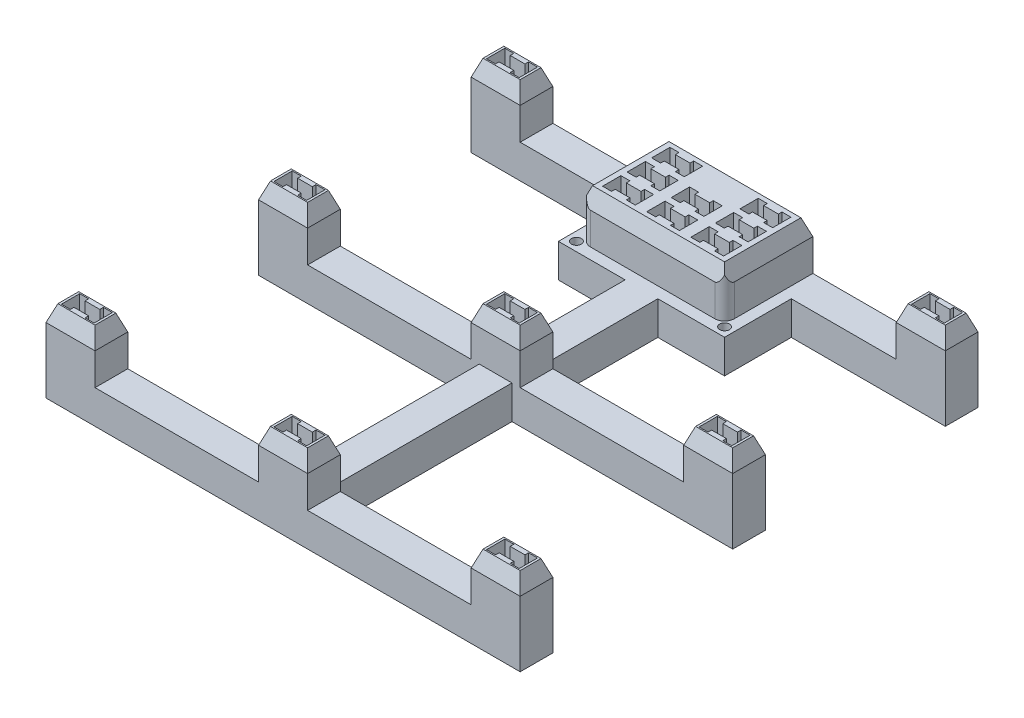
SolidWorks part; units mm, degrees
ref_plane "Front Plane" through (0, 0, 0) normal (0, 0, 1) x (1, 0, 0)
ref_plane "Top Plane" through (0, 0, 0) normal (0, 1, 0) x (1, 0, 0)
ref_plane "Right Plane" through (0, 0, 0) normal (1, 0, 0) x (0, 0, -1)
sketch "Sketch1" plane through (0, 0, 0) normal (0, 1, 0) x (1, 0, 0)
  line L0 (50.5, 130) -> (0, 130)
  line L1 (0, 140) -> (0, 130)
  line L2 (0, 140) -> (145, 140)
  line L4 (145, 130) -> (145, 140)
  line L5 (94.5, 130) -> (145, 130)
  line L6 (50.5, 130) -> (50.5, 113)
  line L7 (50.5, 113) -> (67.5, 113)
  line L8 (94.5, 113) -> (94.5, 130)
  line L9 (77.5, 113) -> (94.5, 113)
  line L10 (67.5, 113) -> (67.5, 75)
  line L11 (77.5, 75) -> (77.5, 113)
  line L12 (67.5, 75) -> (0, 75)
  line L13 (0, 65) -> (0, 75)
  line L14 (0, 65) -> (67.5, 65)
  line L15 (145, 75) -> (77.5, 75)
  line L16 (145, 65) -> (145, 75)
  line L17 (77.5, 65) -> (145, 65)
  line L18 (67.5, 65) -> (67.5, 10)
  line L19 (77.5, 10) -> (77.5, 65)
  line L20 (67.5, 10) -> (0, 10)
  line L21 (0, 10) -> (0, 0)
  line L22 (0, 0) -> (145, 0)
  line L24 (77.5, 10) -> (145, 10)
  line L25 (145, 10) -> (145, 0)
  dimension "D1" = 10
  dimension "D2" = 145
  dimension "D3" = 50.5
  dimension "D4" = 17
  dimension "D5" = 17
  dimension "D6" = 55
  dimension "D7" = 55
extrude "Boss-Extrude1" add sketch "Sketch1" along normal blind 10
sketch "Sketch2" plane through (0, 10, 0) normal (0, 1, 0) x (1, 0, 0)
  line L0 (145, 10) -> (77.5, 10) construction
  line L1 (145, 0) -> (130, 0)
  line L2 (145, 0) -> (145, 10)
  line L3 (145, 10) -> (130, 10)
  line L4 (130, 0) -> (130, 10)
  line L6 (80, 0) -> (65, 0)
  line L7 (80, 0) -> (80, 10)
  line L8 (80, 10) -> (65, 10)
  line L9 (65, 0) -> (65, 10)
  line L10 (67.5, 10) -> (0, 10) construction
  line L11 (0, 0) -> (15, 0)
  line L12 (0, 0) -> (0, 10)
  line L13 (0, 10) -> (15, 10)
  line L14 (15, 0) -> (15, 10)
  line L15 (67.5, 75) -> (0, 75) construction
  line L16 (0, 65) -> (15, 65)
  line L17 (0, 65) -> (0, 75)
  line L18 (0, 75) -> (15, 75)
  line L19 (15, 65) -> (15, 75)
  line L20 (145, 75) -> (77.5, 75) construction
  line L21 (145, 65) -> (130, 65)
  line L22 (145, 65) -> (145, 75)
  line L23 (145, 75) -> (130, 75)
  line L24 (130, 65) -> (130, 75)
  line L25 (77.5, 65) -> (145, 65) construction
  line L26 (80, 65) -> (65, 65)
  line L27 (80, 65) -> (80, 75)
  line L28 (80, 75) -> (65, 75)
  line L29 (65, 65) -> (65, 75)
  line L30 (145, 140) -> (0, 140) construction
  line L31 (145, 130) -> (130, 130)
  line L32 (145, 130) -> (145, 140)
  line L33 (145, 140) -> (130, 140)
  line L34 (130, 130) -> (130, 140)
  line L35 (0, 0) -> (145, 0) construction
  line L36 (0, 130) -> (15, 130)
  line L37 (0, 130) -> (0, 140)
  line L38 (0, 140) -> (15, 140)
  line L39 (15, 130) -> (15, 140)
  line L40 (50.5, 140) -> (94.5, 140)
  line L41 (50.5, 113) -> (94.5, 113)
  line L42 (50.5, 113) -> (50.5, 140)
  line L44 (94.5, 113) -> (94.5, 140)
  point P62 (72.5, 0)
  dimension "D1" = 15
extrude "Boss-Extrude2" add sketch "Sketch2" along normal blind 10
sketch "Sketch3" plane through (0, 20, 0) normal (0, 1, 0) x (1, 0, 0)
  line L0 (0, 140) -> (0, 130) construction
  line L1 (0, 130) -> (15, 130) construction
  line L2 (15, 130) -> (15, 140) construction
  line L3 (15, 140) -> (0, 140) construction
  line L4 (145, 0) -> (145, 10)
  line L5 (145, 10) -> (130, 10)
  line L6 (130, 10) -> (130, 0)
  line L7 (130, 0) -> (145, 0)
  line L8 (145, 0) -> (145, 10)
  line L9 (145, 10) -> (130, 10)
  line L10 (130, 10) -> (130, 0)
  line L11 (130, 0) -> (145, 0)
  line L12 (145, 130) -> (145, 140) construction
  line L13 (145, 140) -> (130, 140) construction
  line L14 (130, 140) -> (130, 130) construction
  line L15 (130, 130) -> (145, 130) construction
  line L16 (145, 65) -> (145, 75) construction
  line L17 (145, 75) -> (130, 75) construction
  line L18 (130, 75) -> (130, 65) construction
  line L19 (130, 65) -> (145, 65) construction
  line L20 (80, 65) -> (80, 75) construction
  line L21 (80, 75) -> (65, 75) construction
  line L22 (65, 75) -> (65, 65) construction
  line L23 (65, 65) -> (80, 65) construction
  line L24 (0, 75) -> (0, 65) construction
  line L25 (0, 65) -> (15, 65) construction
  line L26 (15, 65) -> (15, 75) construction
  line L27 (15, 75) -> (0, 75) construction
  line L28 (0, 10) -> (0, 0) construction
  line L29 (0, 0) -> (15, 0) construction
  line L30 (15, 0) -> (15, 10) construction
  line L31 (15, 10) -> (0, 10) construction
  line L32 (80, 0) -> (80, 10) construction
  line L33 (80, 10) -> (65, 10) construction
  line L34 (65, 10) -> (65, 0) construction
  line L35 (65, 0) -> (80, 0) construction
  line L36 (0, 140) -> (0, 130)
  line L37 (0, 130) -> (15, 130)
  line L38 (15, 130) -> (15, 140)
  line L39 (15, 140) -> (0, 140)
  line L40 (145, 130) -> (145, 140)
  line L41 (145, 140) -> (130, 140)
  line L42 (130, 140) -> (130, 130)
  line L43 (130, 130) -> (145, 130)
  line L44 (145, 65) -> (145, 75)
  line L45 (145, 75) -> (130, 75)
  line L46 (130, 75) -> (130, 65)
  line L47 (130, 65) -> (145, 65)
  line L48 (80, 65) -> (80, 75)
  line L49 (80, 75) -> (65, 75)
  line L50 (65, 75) -> (65, 65)
  line L51 (65, 65) -> (80, 65)
  line L52 (0, 75) -> (0, 65)
  line L53 (0, 65) -> (15, 65)
  line L54 (15, 65) -> (15, 75)
  line L55 (15, 75) -> (0, 75)
  line L56 (0, 10) -> (0, 0)
  line L57 (0, 0) -> (15, 0)
  line L58 (15, 0) -> (15, 10)
  line L59 (15, 10) -> (0, 10)
  line L60 (80, 0) -> (80, 10)
  line L61 (80, 10) -> (65, 10)
  line L62 (65, 10) -> (65, 0)
  line L63 (65, 0) -> (80, 0)
  line L68 (50.5, 140) -> (50.5, 113)
  line L69 (50.5, 113) -> (94.5, 113)
  line L70 (94.5, 113) -> (94.5, 140)
  line L71 (94.5, 140) -> (50.5, 140)
  line L72 (50.5, 140) -> (50.5, 113)
  line L73 (50.5, 113) -> (94.5, 113)
  line L74 (94.5, 113) -> (94.5, 140)
  line L75 (94.5, 140) -> (50.5, 140)
  dimension "D1" = 0
  dimension "D2" = 0
extrude "Boss-Extrude3" add sketch "Sketch3" along normal blind 5 draft 20
sketch "Sketch4" plane through (0, 25, 0) normal (0, 1, 0) x (1, 0, 0)
  line L0 (94.5, 140) -> (50.5, 140) construction
  line L1 (89, 140) -> (56, 140)
  line L2 (89, 140) -> (89, 138.1801)
  line L3 (89, 138.1801) -> (56, 138.1801)
  line L4 (56, 140) -> (56, 138.1801)
  line L5 (92.6802, 138.1801) -> (52.3199, 138.1801) construction
  point P9 (72.5, 140)
  dimension "D1" = 33
extrude "Cut-Extrude1" cut sketch "Sketch4" against normal blind 15
sketch "Sketch5" plane through (0, 25, 0) normal (0, 1, 0) x (1, 0, 0)
  line L1 (142.5, 3.3) -> (132.5, 3.3)
  line L2 (142.5, 3.3) -> (142.5, 6.7)
  line L3 (142.5, 6.7) -> (132.5, 6.7)
  line L4 (132.5, 3.3) -> (132.5, 6.7)
  line L6 (132.5, 5) -> (131.8199, 5) construction
  line L7 (131.8199, 8.1802) -> (131.8199, 1.8199) construction
  line L8 (137.5, 6.7) -> (137.5, 8.1802) construction
  line L9 (143.1802, 8.1802) -> (131.8199, 8.1802) construction
  dimension "D1" = 3.4
  dimension "D2" = 10
extrude "Cut-Extrude2" cut sketch "Sketch5" against normal blind 7.75
sketch "Sketch7" plane through (0, 25, 0) normal (0, 1, 0) x (1, 0, 0)
  line L0 (142.5, 6.7) -> (132.5, 6.7) construction
  line L1 (132.5, 6.7) -> (135.25, 6.7)
  line L2 (132.5, 6.7) -> (132.5, 7.8)
  line L3 (132.5, 7.8) -> (135.25, 7.8)
  line L4 (135.25, 6.7) -> (135.25, 7.8)
  line L5 (132.5, 6.7) -> (132.5, 3.3) construction
  line L6 (132.5, 6.7) -> (132.5, 3.3) construction
  line L8 (132.5, 3.3) -> (135.25, 3.3)
  line L9 (132.5, 3.3) -> (132.5, 2.2)
  line L10 (132.5, 2.2) -> (135.25, 2.2)
  line L11 (135.25, 3.3) -> (135.25, 2.2)
  line L12 (142.5, 6.7) -> (139.75, 6.7)
  line L13 (142.5, 6.7) -> (142.5, 7.8)
  line L14 (142.5, 7.8) -> (139.75, 7.8)
  line L15 (139.75, 6.7) -> (139.75, 7.8)
  line L16 (142.5, 3.3) -> (139.75, 3.3)
  line L17 (142.5, 3.3) -> (142.5, 2.2)
  line L18 (142.5, 2.2) -> (139.75, 2.2)
  line L19 (139.75, 3.3) -> (139.75, 2.2)
  dimension "D1" = 2.75
  dimension "D2" = 1.1
extrude "Cut-Extrude4" cut sketch "Sketch7" against normal up to surface (7.75 mm away) up to face at (137.5, 17.25, -5)
pattern_linear "LPattern1" count 3 spacing 65 along (-1, 0, 0) count 3 spacing 65 along (0, 0, -1) skipping (1, 2) of "Cut-Extrude2", "Cut-Extrude4"
sketch "Sketch6" plane through (0, 25, 0) normal (0, 1, 0) x (1, 0, 0)
  line L21 (91, 117.3) -> (81, 117.3)
  line L22 (91, 117.3) -> (91, 120.7)
  line L23 (91, 120.7) -> (81, 120.7)
  line L36 (81, 117.3) -> (81, 120.7)
  line L37 (67.5, 117.3) -> (67.5, 120.7)
  line L39 (77.5, 117.3) -> (67.5, 117.3)
  line L68 (50.5, 113) -> (94.5, 113) construction
  line L69 (94.5, 113) -> (94.5, 140) construction
  line L70 (77.5, 120.7) -> (67.5, 120.7)
  line L71 (77.5, 117.3) -> (77.5, 120.7)
  line L72 (54, 117.3) -> (54, 120.7)
  line L73 (64, 117.3) -> (54, 117.3)
  line L74 (64, 120.7) -> (54, 120.7)
  line L75 (64, 117.3) -> (64, 120.7)
  line L76 (67.5, 124.8) -> (67.5, 128.2)
  line L77 (77.5, 124.8) -> (67.5, 124.8)
  line L78 (77.5, 128.2) -> (67.5, 128.2)
  line L79 (77.5, 124.8) -> (77.5, 128.2)
  line L80 (54, 124.8) -> (54, 128.2)
  line L81 (64, 124.8) -> (54, 124.8)
  line L82 (64, 128.2) -> (54, 128.2)
  line L83 (64, 124.8) -> (64, 128.2)
  line L84 (67.5, 132.3) -> (67.5, 135.7) [skipped]
  line L85 (77.5, 132.3) -> (67.5, 132.3) [skipped]
  line L86 (77.5, 135.7) -> (67.5, 135.7) [skipped]
  line L87 (77.5, 132.3) -> (77.5, 135.7) [skipped]
  line L88 (54, 132.3) -> (54, 135.7)
  line L89 (64, 132.3) -> (54, 132.3)
  line L90 (64, 135.7) -> (54, 135.7)
  line L91 (64, 132.3) -> (64, 135.7)
  line L92 (81, 124.8) -> (81, 128.2)
  line L93 (91, 124.8) -> (81, 124.8)
  line L94 (91, 128.2) -> (81, 128.2)
  line L95 (91, 124.8) -> (91, 128.2)
  line L96 (81, 132.3) -> (81, 135.7)
  line L97 (91, 132.3) -> (81, 132.3)
  line L98 (91, 135.7) -> (81, 135.7)
  line L99 (91, 132.3) -> (91, 135.7)
  point P40 (91, 119)
  point P45 (86, 117.3)
  dimension "D1" = 10
  dimension "D2" = 3.4
  dimension "D3" = 6
  dimension "D4" = 8.5
  dimension "D5" = 3
  dimension "D6" = 3
extrude "Cut-Extrude3" cut sketch "Sketch6" against normal blind 7.75
fillet "Fillet1" radius 3 2 edges at (50.5, 10, -113) (94.5, 10, -113)
sketch "Sketch9" plane through (0, 25, 0) normal (0, 1, 0) x (1, 0, 0)
  line L0 (81, 120.7) -> (83.75, 120.7)
  line L1 (81, 120.7) -> (81, 121.8)
  line L2 (81, 121.8) -> (83.75, 121.8)
  line L3 (83.75, 120.7) -> (83.75, 121.8)
  line L4 (81, 117.3) -> (83.75, 117.3)
  line L5 (81, 117.3) -> (81, 116.2)
  line L6 (81, 116.2) -> (83.75, 116.2)
  line L7 (83.75, 117.3) -> (83.75, 116.2)
  line L8 (91, 120.7) -> (88.25, 120.7)
  line L9 (91, 120.7) -> (91, 121.8)
  line L10 (91, 121.8) -> (88.25, 121.8)
  line L11 (88.25, 120.7) -> (88.25, 121.8)
  line L12 (91, 117.3) -> (88.25, 117.3)
  line L13 (91, 117.3) -> (91, 116.2)
  line L14 (91, 116.2) -> (88.25, 116.2)
  line L15 (88.25, 117.3) -> (88.25, 116.2)
  line L16 (81, 120.7) -> (81, 117.3) construction
  line L17 (81, 117.3) -> (91, 117.3) construction
  line L18 (91, 120.7) -> (81, 120.7) construction
  dimension "D1" = 2.75
  dimension "D2" = 1.1
extrude "Cut-Extrude5" cut sketch "Sketch9" against normal up to surface (7.75 mm away) up to face at (86, 17.25, -119)
pattern_linear "LPattern2" count 3 spacing 13.5 along (-1, 0, 0) count 3 spacing 7.5 along (0, 0, -1) skipping (1, 2) of "Cut-Extrude5"
sketch "Sketch10" plane through (0, 10, 0) normal (0, 1, 0) x (1, 0, 0)
  line L0 (50.5, 130) -> (47.1, 130)
  line L1 (15, 130) -> (50.5, 130) construction
  line L2 (47.1, 130) -> (47.1, 109.6)
  line L3 (47.1, 109.6) -> (67.5, 109.6)
  line L4 (67.5, 113) -> (67.5, 75) construction
  line L5 (67.5, 109.6) -> (67.5, 113)
  line L6 (77.5, 113) -> (77.5, 109.6)
  line L7 (77.5, 75) -> (77.5, 113) construction
  line L8 (77.5, 109.6) -> (97.9, 109.6)
  line L9 (97.9, 109.6) -> (97.9, 130)
  line L10 (94.5, 130) -> (130, 130) construction
  line L11 (97.9, 130) -> (94.5, 130)
  line L12 (94.5, 116) -> (94.5, 140) construction
  line L13 (53.5, 113) -> (91.5, 113) construction
  line L14 (50.5, 140) -> (50.5, 116) construction
  line L15 (94.5, 116) -> (94.5, 130)
  line L16 (53.5, 113) -> (67.5, 113)
  line L17 (50.5, 130) -> (50.5, 116)
  line L18 (77.5, 113) -> (91.5, 113)
  arc A0 (93.6213, 113.8787) -> (94.5, 116) centre (91.5, 116) ccw construction
  arc A1 (91.5, 113) -> (93.6213, 113.8787) centre (91.5, 116) ccw construction
  arc A2 (51.3787, 113.8787) -> (53.5, 113) centre (53.5, 116) ccw construction
  arc A3 (50.5, 116) -> (51.3787, 113.8787) centre (53.5, 116) ccw construction
  arc A4 (93.6213, 113.8787) -> (94.5, 116) centre (91.5, 116) ccw
  arc A5 (91.5, 113) -> (93.6213, 113.8787) centre (91.5, 116) ccw
  arc A6 (51.3787, 113.8787) -> (53.5, 113) centre (53.5, 116) ccw
  arc A7 (50.5, 116) -> (51.3787, 113.8787) centre (53.5, 116) ccw
  dimension "D1" = 3.4
extrude "Boss-Extrude4" add sketch "Sketch10" against normal up to surface (10 mm away) up to face at (72.5, 0, -80.106)
sketch "Sketch11" plane through (0, 0, 0) normal (0, -1, 0) x (1, 0, 0)
  line L0 (95.1511, -112.3491) -> (49.8489, -112.3491) construction
  line L1 (97.9, -130) -> (97.9, -109.6) construction
  line L2 (97.9, -109.6) -> (77.5, -109.6) construction
  line L3 (47.1, -109.6) -> (47.1, -130) construction
  circle A0 centre (95.1511, -112.3491) radius 1.5
  circle A1 centre (49.8489, -112.3491) radius 1.5
  dimension "D1" = 3
  dimension "D2" = 2.7489
  dimension "D3" = 2.7491
  dimension "D4" = 2.7489
extrude "Cut-Extrude6" cut sketch "Sketch11" against normal up to next
other "Move Face1" face at (105, 10, -5) face at (40, 10, -5) face at (72.5, 10, -37.5) face at (105, 10, -70) face at (40, 10, -70) face at (95.1511, 10, -110.8491) parameters "D1"=0.25
